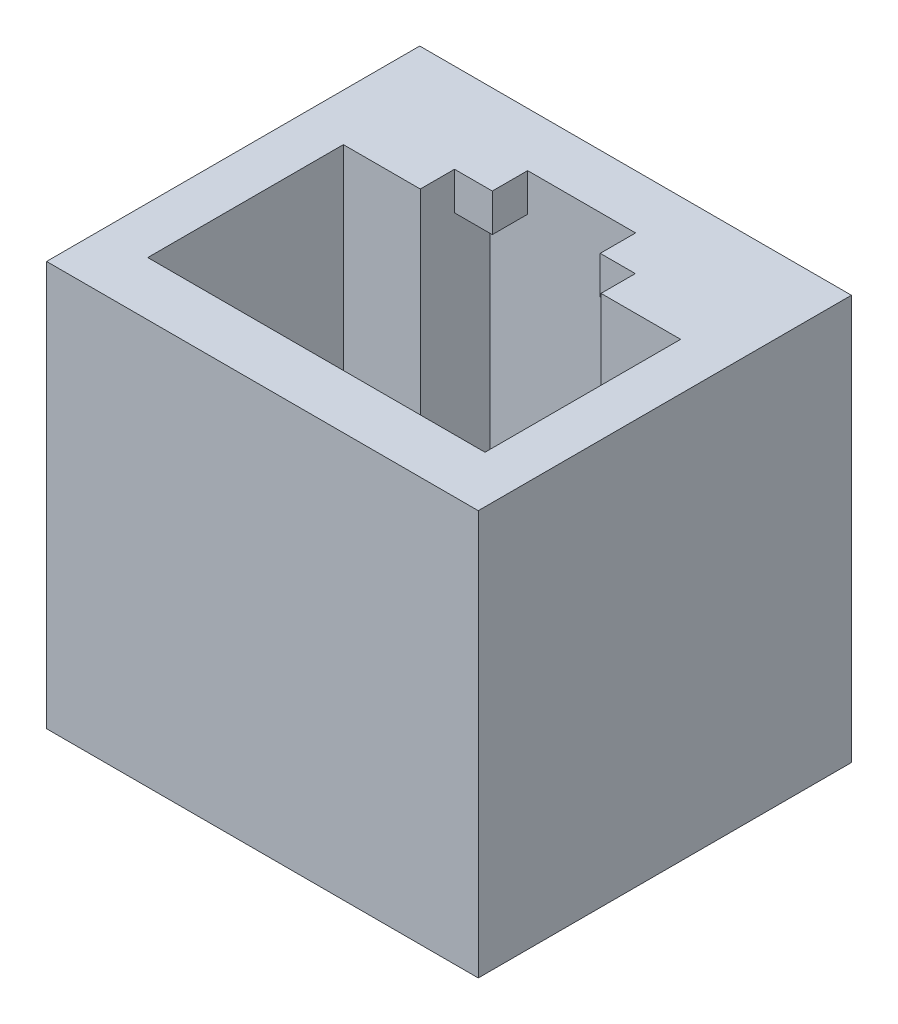
SolidWorks part; units mm, degrees
ref_plane "Front Plane" through (0, 0, 0) normal (0, 0, 1) x (1, 0, 0)
ref_plane "Top Plane" through (0, 0, 0) normal (0, 1, 0) x (1, 0, 0)
ref_plane "Right Plane" through (0, 0, 0) normal (1, 0, 0) x (0, 0, -1)
sketch "Sketch1" plane through (0, 0, 0) normal (0, 1, 0) x (1, 0, 0)
  line L0 (0, 0) -> (0, 7.25)
  line L1 (0, 7.25) -> (2.85, 7.25)
  line L2 (2.85, 7.25) -> (2.85, 8.52)
  line L3 (2.85, 8.52) -> (4.25, 8.52)
  line L4 (4.25, 8.52) -> (4.25, 9.83)
  line L5 (4.25, 9.83) -> (8.25, 9.83)
  line L6 (8.25, 9.83) -> (8.25, 8.52)
  line L7 (8.25, 8.52) -> (9.55, 8.52)
  line L8 (9.55, 8.52) -> (9.55, 7.25)
  line L9 (9.55, 7.25) -> (12.5, 7.25)
  line L10 (12.5, 7.25) -> (12.5, 0)
  line L11 (12.5, 0) -> (0, 0)
  line L13 (-1.75, 11.83) -> (14.25, 11.83)
  line L14 (-1.75, 11.83) -> (-1.75, -2)
  line L15 (-1.75, -2) -> (14.25, -2)
  line L16 (14.25, 11.83) -> (14.25, -2)
  point P3 (2.85, 7.885)
  point P14 (6.25, 0)
  point P15 (6.25, 9.83)
  dimension "D1" = 12.5
  dimension "D2" = 7.25
  dimension "D3" = 8.52
  dimension "D4" = 9.83
  dimension "D5" = 7.25
  dimension "D6" = 6.7
  dimension "D7" = 4
  dimension "D8" = 2.85
  dimension "D9" = 1.75
  dimension "D10" = 2
  dimension "D11" = 1.75
  dimension "D12" = 2
extrude "Boss-Extrude1" add sketch "Sketch1" along normal blind 25
sketch "Sketch2" plane through (0, 0, 0) normal (0, -1, 0) x (1, 0, 0)
  line L0 (0, 0) -> (12.5, 0) construction
  line L1 (12.5, -7.25) -> (11.5, -7.25)
  line L2 (12.5, -7.25) -> (12.5, -6.1)
  line L3 (12.5, -6.1) -> (11.5, -6.1)
  line L4 (11.5, -7.25) -> (11.5, -6.1)
  line L5 (0, -7.25) -> (1, -7.25)
  line L6 (0, -7.25) -> (0, -6.1)
  line L7 (0, -6.1) -> (1, -6.1)
  line L8 (1, -7.25) -> (1, -6.1)
  point P12 (0.5, -6.1)
  dimension "D1" = 6.1
  dimension "D2" = 6.1
  dimension "D3" = 1
  dimension "D4" = 1
extrude "Boss-Extrude3" add sketch "Sketch2" against normal offset from surface (16.73 mm away) 16.73 up to face at (6.25, 0, -4.915)
sketch "Sketch3" plane through (0, 0, 0) normal (0, -1, 0) x (1, 0, 0)
  line L0 (2.85, -8.52) -> (2.85, -7.25) construction
  line L1 (4.25, -8.52) -> (2.85, -8.52)
  line L2 (4.25, -8.52) -> (4.25, -9.83)
  line L3 (4.25, -9.83) -> (2.85, -9.83)
  line L4 (2.85, -8.52) -> (2.85, -9.83)
  line L5 (8.25, -8.52) -> (9.55, -8.52)
  line L6 (8.25, -8.52) -> (8.25, -9.83)
  line L7 (8.25, -9.83) -> (9.55, -9.83)
  line L8 (9.55, -8.52) -> (9.55, -9.83)
  line L9 (8.25, -9.83) -> (4.25, -9.83) construction
  line L10 (9.55, -7.25) -> (9.55, -8.52) construction
extrude "Cut-Extrude1" cut sketch "Sketch3" against normal blind 23.6
sketch "Sketch5" plane through (0, 0, 0) normal (0, -1, 0) x (1, 0, 0)
  line L1 (-1.75, 2) -> (14.25, 2)
  line L2 (-1.75, 2) -> (-1.75, -11.83)
  line L3 (-1.75, -11.83) -> (14.25, -11.83)
  line L4 (14.25, 2) -> (14.25, -11.83)
extrude "Cut-Extrude2" cut sketch "Sketch5" against normal blind 10
